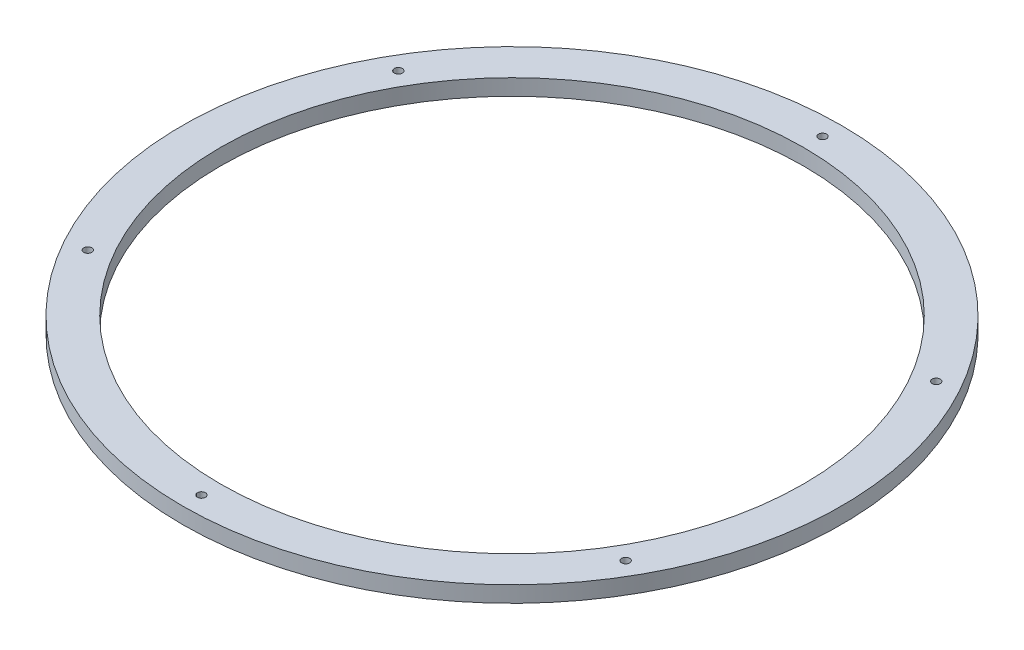
SolidWorks part; units mm, degrees
ref_plane "Front Plane" through (0, 0, 0) normal (0, 0, 1) x (1, 0, 0)
ref_plane "Top Plane" through (0, 0, 0) normal (0, 1, 0) x (1, 0, 0)
ref_plane "Right Plane" through (0, 0, 0) normal (1, 0, 0) x (0, 0, -1)
sketch "Sketch1" plane through (0, 0, 0) normal (0, 1, 0) x (1, 0, 0)
  circle A0 centre (0, 0) radius 130
  circle A1 centre (0, 0) radius 115
  circle A2 centre (0, 122.5) radius 1.5875
  circle A3 centre (106.0881, 61.25) radius 1.5875
  circle A4 centre (106.0881, -61.25) radius 1.5875
  circle A5 centre (0, -122.5) radius 1.5875
  circle A6 centre (-106.0881, -61.25) radius 1.5875
  circle A7 centre (-106.0881, 61.25) radius 1.5875
  point P19 (0, 0)
  dimension "D1" = 260
  dimension "D4" = 3.175
  dimension "D3" = 122.5
  dimension "D2" = 15
  dimension "D5" = 6
extrude "Boss-Extrude1" add sketch "Sketch1" along normal blind 6.35 contours A0 A7 A6 A5 A4 A3 A2 A1
equation "\"D3@Sketch1\"=260/2 - 7.5"
